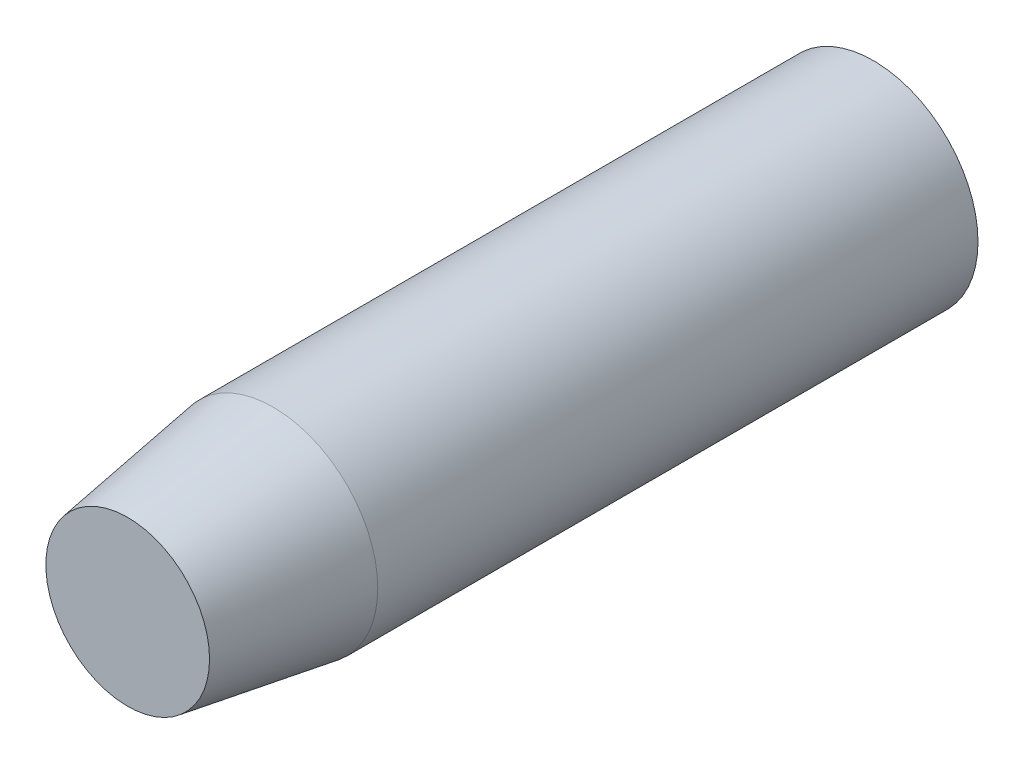
SolidWorks part; units mm, degrees
material "6061-T6 (SS)"
ref_plane "Front Plane" through (0, 0, 0) normal (0, 0, 1) x (1, 0, 0)
ref_plane "Top Plane" through (0, 0, 0) normal (0, 1, 0) x (1, 0, 0)
ref_plane "Right Plane" through (0, 0, 0) normal (1, 0, 0) x (0, 0, -1)
sketch "Sketch1" plane through (0, 0, 0) normal (0, 0, 1) x (1, 0, 0)
  circle A0 centre (0, 0) radius 18.2563
  dimension "D1" = 36.5125
extrude "Boss-Extrude1" add sketch "Sketch1" along normal mid plane 130.175
chamfer "Chamfer1" distance 25.4 distance2 3.9688 1 edges at (18.2563, 0, 65.0875)
